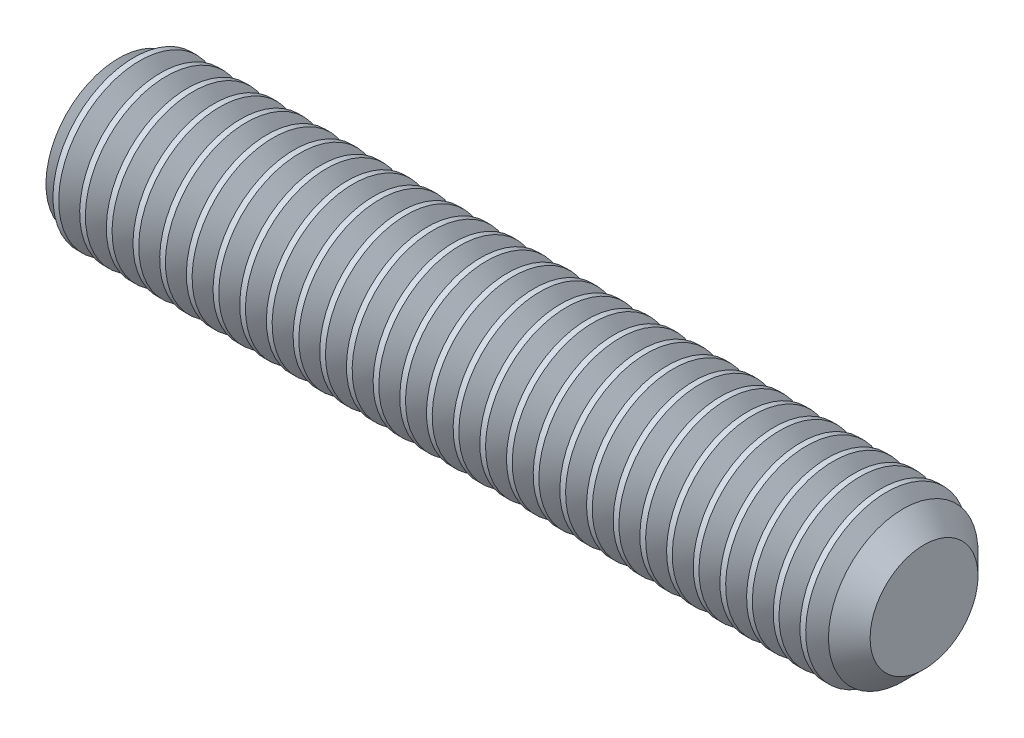
SolidWorks part; units mm, degrees
ref_plane "Plane1" through (0, 0, 0) normal (0, 0, 1) x (1, 0, 0)
ref_plane "Plane2" through (0, 0, 0) normal (0, 1, 0) x (1, 0, 0)
ref_plane "Plane3" through (0, 0, 0) normal (1, 0, 0) x (0, 0, -1)
revolve "BaseBody" add sketch "BodySke" angle 360 about L5
sketch "BodySke" plane through (0, 0, 0) normal (0, 0, 1) x (1, 0, 0)
  line L0 (0, 0) -> (0, 2.4455)
  line L1 (0, 2.4455) -> (0.3201, 3)
  line L2 (0.3201, 3) -> (29, 3)
  line L3 (29, 3) -> (30, 2)
  line L4 (30, 0) -> (0, 0)
  line L5 (-12.7, 0) -> (88.9, 0) construction
  line L6 (30, 2) -> (30, 0)
  line L7 (30, 2) -> (30, 11.525) construction
  line L8 (0, -2.4455) -> (0.3201, -3) construction
  line L9 (1, 15.875) -> (1, -3.175) construction
  line L10 (29, -3) -> (30, -2) construction
  dimension "Length" = 30
  dimension "Diameter" = 6
  dimension "Drive_ch_ang" = 60
  dimension "Minor_dia" = 4.891
  dimension "Cup_nose_ang" = 45
  dimension "Cup_dia" = 4
  dimension "Advance" = 1
cosmetic thread "ThreadCosmetic" [suppressed] parameters "Thread_minor"=4.891
sketch "Sketch2" plane through (0, 0, 0) normal (-1, 0, 0) x (0, 0, 1)
  line L0 (0.866, 1.5) -> (-0.866, 1.5)
  line L1 (-0.866, 1.5) -> (-1.7321, 0)
  line L2 (0.866, 1.5) -> (1.7321, 0)
  line L3 (0.866, -1.5) -> (1.7321, 0)
  line L4 (0.866, -1.5) -> (-0.866, -1.5)
  line L5 (-0.866, -1.5) -> (-1.7321, 0)
  dimension "Hex_size" = 3
  dimension "D2" = 1.5
  dimension "D3" = 1.5
extrude "Hex" cut sketch "Sketch2" against normal blind 3.5
sketch "ThdSchSke" plane through (0, 0, 0) normal (0, 0, 1) x (1, 0, 0)
  line L0 (0.3201, -2.4455) -> (-0.0681, -3)
  line L1 (0.3201, -2.4455) -> (0.7084, -3)
  line L2 (0.7084, -3) -> (0.7084, -3.75)
  line L3 (-3.175, 0) -> (5.1513, 0) construction
  line L5 (0.7084, -3.75) -> (-0.0681, -3.75)
  line L6 (-0.0681, -3.75) -> (-0.0681, -3)
  line L8 (0.3201, 3) -> (0.3201, -3) construction
  dimension "Thread_minor" = 4.891
  dimension "Diameter" = 6
  dimension "SideAngle" = 55
  dimension "VeeAngle" = 70
  dimension "Overcut" = 7.5
revolve "ThreadSchematic" cut sketch "ThdSchSke" angle 360 about L3
pattern_linear "ThdSchPat" count 30 spacing 0.989 along (1, 0, 0) of "ThreadSchematic"
equation "\"D2@Sketch2\" = \"Hex_size@Sketch2\" / 2"
equation "\"D3@Sketch2\" = \"Hex_size@Sketch2\" / 2"
equation "\"Thread_minor@ThreadCosmetic\" = \"Minor_dia@BodySke\""
equation "\"Thread_minor@ThdSchSke\" = \"Thread_minor@ThreadCosmetic\""
equation "\"Diameter@ThdSchSke\" = \"Diameter@BodySke\""
equation "\"Overcut@ThdSchSke\" = \"Diameter@BodySke\" * 1.25"
equation "\"Num_threads@ThdSchPat\" = int( (\"Length@BodySke\" - ( ( ( \"Diameter@BodySke\" - \"Minor_dia@BodySke\" ) * 0.5 ) / tan( \"Drive_ch_ang@BodySke\" * 0.017453292 ) ) - ( ( ( \"Diameter@BodySke\" - \"Cup_dia@BodySke\" ) * 0.5 ) * tan( \"Cup_nose_ang@BodySke\" * 0.017453292 ) ) ) / \"Advance@BodySke\" + 0.999 )  + 1"
equation "\"Advance@ThdSchPat\" = (\"Length@BodySke\" - ( ( ( \"Diameter@BodySke\" - \"Minor_dia@BodySke\" ) * 0.5 ) / tan( \"Drive_ch_ang@BodySke\" * 0.017453292 ) ) - ( ( ( \"Diameter@BodySke\" - \"Cup_dia@BodySke\" ) * 0.5 ) * tan( \"Cup_nose_ang@BodySke\" * 0.017453292 ) ) ) /  (\"Num_threads@ThdSchPat\" - 1) 'relax it"
equation "' \"Num_threads@ThdSchPat\" = \"Num_threads@ThdSchPat\" - sgn( \"Num_threads@ThdSchPat\" - 1) '---chamfered tips only---"
